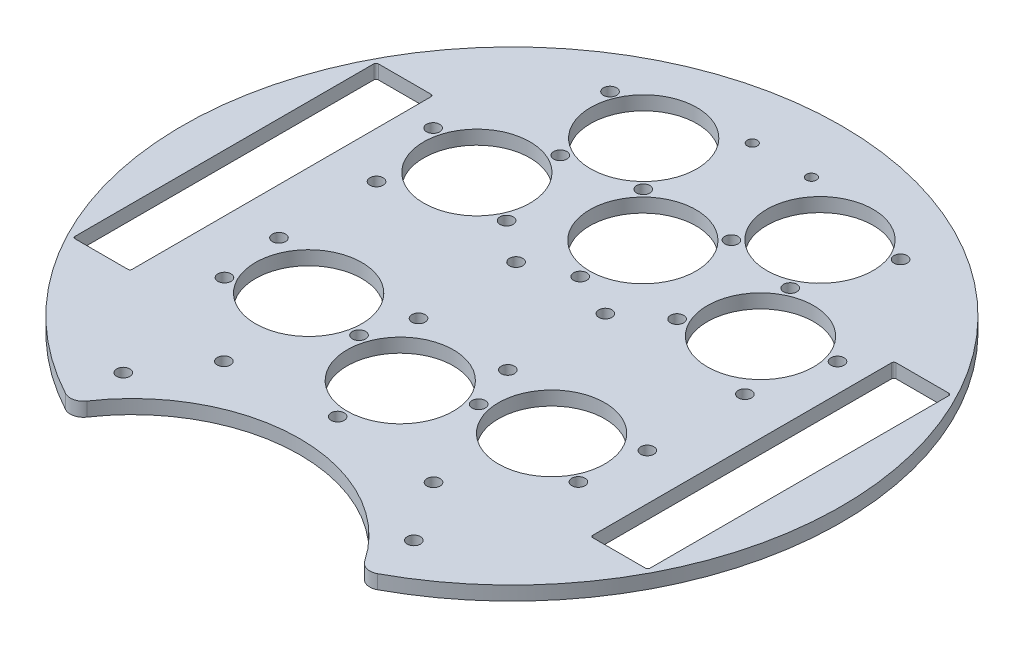
SolidWorks part; units mm, degrees
ref_plane "Front Plane" through (0, 0, 0) normal (0, 0, 1) x (1, 0, 0)
ref_plane "Top Plane" through (0, 0, 0) normal (0, 1, 0) x (1, 0, 0)
ref_plane "Right Plane" through (0, 0, 0) normal (1, 0, 0) x (0, 0, -1)
sketch "Sketch1" plane through (0, 0, 0) normal (0, 1, 0) x (1, 0, 0)
  line L0 (0, 0) -> (-51.5062, -59.2511) construction
  line L1 (0, 86.2583) -> (0, -96.8543) construction
  line L2 (-26.1633, 37.1696) -> (-32.2721, 24.2954) construction
  line L3 (-32.9956, -67.352) -> (0, -86.402) construction
  line L4 (32.9956, -67.352) -> (0, -86.402) construction
  line L5 (0, 0) -> (-13.6167, -50.8184) construction
  line L6 (-33.3347, -42.5389) -> (-41.6896, -52.1501) construction
  line L7 (-32.2721, 24.2954) -> (-46.0115, 28.0759) construction
  line L8 (-83.3992, 0) -> (107.0959, 0) construction
  line L9 (52.4101, -34) -> (52.4101, 34)
  line L10 (-64.9101, -34.5) -> (-52.9101, -34.5)
  line L11 (-65.4101, -34) -> (-65.4101, 34)
  line L12 (-64.9101, 34.5) -> (-52.9101, 34.5)
  line L13 (-52.4101, -34) -> (-52.4101, 34)
  line L14 (64.9101, 34.5) -> (52.9101, 34.5)
  line L15 (65.4101, -34) -> (65.4101, 34)
  line L16 (64.9101, -34.5) -> (52.9101, -34.5)
  line L17 (0, 0) -> (13.6167, -50.8184) construction
  line L18 (-33.3347, -42.5389) -> (-37.4856, -38.9306) construction
  line L19 (0, 0) -> (-95.645, -6.6882) construction
  line L20 (-37.4856, -38.9306) -> (-45.4633, -48.1079) construction
  line L21 (-42.5389, 33.3347) -> (-51.7162, 41.3124) construction
  line L22 (33.3347, -42.5389) -> (41.6896, -52.1501) construction
  line L23 (37.4856, -38.9306) -> (45.4633, -48.1079) construction
  line L24 (-38.9306, 37.4856) -> (-42.5389, 33.3347) construction
  line L25 (-38.9306, 37.4856) -> (-48.5418, 45.8405) construction
  line L26 (33.3347, -42.5389) -> (37.4856, -38.9306) construction
  line L27 (38.9306, 37.4856) -> (42.5389, 33.3347) construction
  line L28 (42.5389, 33.3347) -> (51.7162, 41.3124) construction
  line L29 (-18.4555, -45.8919) -> (-23.0541, -33.9225) construction
  line L30 (-23.0541, -33.9225) -> (-17.92, -31.9499) construction
  line L31 (38.9306, 37.4856) -> (48.5418, 45.8405) construction
  line L32 (-58.9101, -34.5) -> (-58.9101, 19.5819) construction
  line L35 (-13.6167, -50.8184) -> (-25.1096, -20.9046) construction
  line L37 (-13.3214, -43.9193) -> (-17.92, -31.9499) construction
  line L38 (13.6167, -50.8184) -> (24.3327, -22.8079) construction
  line L39 (18.4555, -45.8919) -> (23.0541, -33.9225) construction
  line L40 (23.0541, -33.9225) -> (17.92, -31.9499) construction
  line L41 (13.3214, -43.9193) -> (17.92, -31.9499) construction
  line L42 (-58.5537, 0) -> (91.2411, 0) construction
  line L46 (0, 34.6626) -> (0, -51.647) construction
  line L47 (-37.1849, 0) -> (48.113, 0) construction
  line L48 (0, 49.2959) -> (0, -33.0158) construction
  arc A0 (35.4973, -66.0677) -> (-35.4973, -66.0677) centre (0, 0) ccw
  arc A1 (31.59, -65.1022) -> (-31.59, -65.1022) centre (0, -86.402) ccw
  circle A2 centre (0, 0) radius 74 construction
  circle A3 centre (-13.6089, -21.1831) radius 1.5
  circle A4 centre (27.6453, -18.6148) radius 14.218 construction
  arc A5 (40.0385, -63.4186) -> (41.6896, -52.1501) centre (36.0347, -57.0767) ccw construction
  arc A6 (57.2141, -48.4928) -> (45.4633, -48.1079) centre (51.4912, -43.6452) cw construction
  circle A7 centre (27.6453, -18.6148) radius 12.095
  circle A8 centre (-46.0115, 28.0759) radius 1.5
  circle A9 centre (13.6089, -21.1831) radius 1.5
  circle A10 centre (23.8525, -41.6946) radius 1.5
  arc A11 (-57.2141, -48.4928) -> (-45.4633, -48.1079) centre (-51.4912, -43.6452) ccw construction
  arc A12 (-40.0385, -63.4186) -> (-41.6896, -52.1501) centre (-36.0347, -57.0767) cw construction
  arc A13 (-5.2684, -48.6449) -> (-13.3214, -43.9193) centre (-6.3241, -41.2196) cw construction
  arc A14 (-21.2728, -54.7938) -> (-18.4555, -45.8919) centre (-25.4604, -48.5717) ccw construction
  circle A15 centre (-26.2497, -27.6477) radius 12.095 construction
  circle A16 centre (-26.2497, -27.6477) radius 14.25 construction
  arc A17 (21.2728, -54.7938) -> (18.4555, -45.8919) centre (25.4604, -48.5717) cw construction
  arc A18 (5.2684, -48.6449) -> (13.3214, -43.9193) centre (6.3241, -41.2196) ccw construction
  circle A19 centre (-41.9101, 11.1) radius 1.5
  circle A20 centre (-41.9101, -11.1) radius 1.5
  circle A21 centre (-10.1601, -11.1) radius 1.5
  circle A22 centre (-10.1601, 11.1) radius 1.5
  circle A23 centre (10.1601, 11.1) radius 1.5
  circle A24 centre (10.1601, -11.1) radius 1.5
  circle A25 centre (41.9101, -11.1) radius 1.5
  circle A26 centre (41.9101, 11.1) radius 1.5
  circle A27 centre (-23.8525, -41.6946) radius 1.5
  circle A28 centre (19.3979, 18.1866) radius 1.5
  circle A29 centre (0, 29.7936) radius 12.095
  circle A30 centre (0, -25.4092) radius 12.095
  circle A31 centre (-40.2774, -25.1402) radius 1.5
  circle A32 centre (40.2774, -25.1402) radius 1.5
  circle A33 centre (6.731, 61.4226) radius 1.143
  circle A34 centre (-6.731, 61.4226) radius 1.143
  arc A35 (-5.8539, 64.7449) -> (5.8576, 64.7385) centre (0, 61.4226) cw construction
  arc A36 (5.8576, 64.7385) -> (5.8576, 58.1067) centre (6.731, 61.4226) cw construction
  arc A37 (-5.8539, 58.1002) -> (-5.8539, 64.7449) centre (-6.731, 61.4226) cw construction
  arc A38 (5.8576, 58.1067) -> (-5.8539, 58.1002) centre (0, 61.4226) cw construction
  circle A39 centre (26.2497, -27.6477) radius 14.25 construction
  circle A42 centre (32.2721, 24.2954) radius 14.25 construction
  circle A43 centre (-32.2721, 24.2954) radius 12.095
  circle A44 centre (26.1633, 37.1696) radius 1.5
  circle A45 centre (32.2721, 24.2954) radius 12.095
  circle A46 centre (-27.6453, -18.6148) radius 12.095
  circle A47 centre (26.2497, -27.6477) radius 12.095 construction
  circle A48 centre (46.0115, 28.0759) radius 1.5
  circle A49 centre (-20.0544, 50.0438) radius 12.095
  circle A50 centre (10.0272, 39.9187) radius 1.5
  arc A51 (-35.4973, -66.0677) -> (-31.59, -65.1022) centre (-34.0774, -63.425) ccw
  arc A52 (35.4973, -66.0677) -> (31.59, -65.1022) centre (34.0774, -63.425) cw
  circle A53 centre (0, -39.6592) radius 1.5
  circle A54 centre (-32.2721, 24.2954) radius 14.25 construction
  circle A55 centre (-10.0272, 39.9187) radius 1.5
  circle A56 centre (20.0544, 50.0438) radius 14.25 construction
  circle A57 centre (20.0544, 50.0438) radius 12.095
  circle A58 centre (0, 29.7936) radius 14.25 construction
  circle A59 centre (-33.0597, -55.3832) radius 1.5
  circle A60 centre (-33.0597, 55.3832) radius 1.5
  circle A61 centre (33.0597, -55.3832) radius 1.5
  circle A62 centre (0, 15.5436) radius 1.5
  circle A63 centre (-26.1633, 37.1696) radius 1.5
  circle A64 centre (0, 0) radius 64.5 construction
  circle A65 centre (-19.3979, 18.1866) radius 1.5
  circle A66 centre (-20.0544, 50.0438) radius 14.25 construction
  circle A67 centre (33.0597, 55.3832) radius 1.5
  arc A68 (-48.475, 57.2291) -> (-48.5418, 45.8405) centre (-43.6275, 51.5062) ccw construction
  arc A69 (-63.4062, 40.0581) -> (-51.7162, 41.3124) centre (-57.0643, 36.0543) cw construction
  arc A70 (63.4062, 40.0581) -> (51.7162, 41.3124) centre (57.0643, 36.0543) ccw construction
  arc A71 (48.475, 57.2291) -> (48.5418, 45.8405) centre (43.6275, 51.5062) cw construction
  arc A72 (-65.4101, -34) -> (-64.9101, -34.5) centre (-64.9101, -34) ccw
  arc A73 (-52.4101, -34) -> (-52.9101, -34.5) centre (-52.9101, -34) cw
  circle A74 centre (-27.6453, -18.6148) radius 14.218 construction
  arc A75 (-52.4101, 34) -> (-52.9101, 34.5) centre (-52.9101, 34) ccw
  arc A76 (-65.4101, 34) -> (-64.9101, 34.5) centre (-64.9101, 34) cw
  arc A77 (65.4101, 34) -> (64.9101, 34.5) centre (64.9101, 34) ccw
  circle A78 centre (0, -25.4092) radius 14.25 construction
  arc A79 (52.4101, 34) -> (52.9101, 34.5) centre (52.9101, 34) cw
  arc A80 (52.4101, -34) -> (52.9101, -34.5) centre (52.9101, -34) ccw
  arc A81 (65.4101, -34) -> (64.9101, -34.5) centre (64.9101, -34) cw
  point P14 (-62.6039, 0)
  point P23 (62.6039, 0)
  point P35 (-31.5178, -45.012)
  point P40 (-46.7211, -26.9744)
  point P45 (-23.8153, 50.3782)
  point P48 (0, -25.4092)
  point P84 (-20.4871, -32.9362)
  point P154 (0, 58.1002)
  dimension "D1" = 150
  dimension "D2" = 76.2
  dimension "D10" = 148
  dimension "D13" = 3
  dimension "D14" = 3
  dimension "D22" = 2.286
  dimension "D20" = 3
  dimension "D11" = 24.19
  dimension "D12" = 28.436
  dimension "D24" = 28.5
  dimension "D21" = 24.19
  dimension "D25" = 28.5
  dimension "D26" = 28.5
  dimension "D29" = 28.5
  dimension "D8" = 28.5
  dimension "D16" = 6
  dimension "D3" = 120
  dimension "D9" = 30
  dimension "D6" = 12.8224
  dimension "D17" = 22.2
  dimension "D19" = 22.2
  dimension "D15" = 10.5
  dimension "D18" = 31.75
  dimension "D23" = 13.462
  dimension "D31" = 100
  dimension "D27" = 45
  dimension "D28" = 12.735
  dimension "D4" = 13
  dimension "D30" = 170
extrude "Boss-Extrude2" add sketch "Sketch1" along normal blind 3.175
fillet "Fillet1" [suppressed] radius 2
equation "\"D10@Sketch1\"=150-2"
